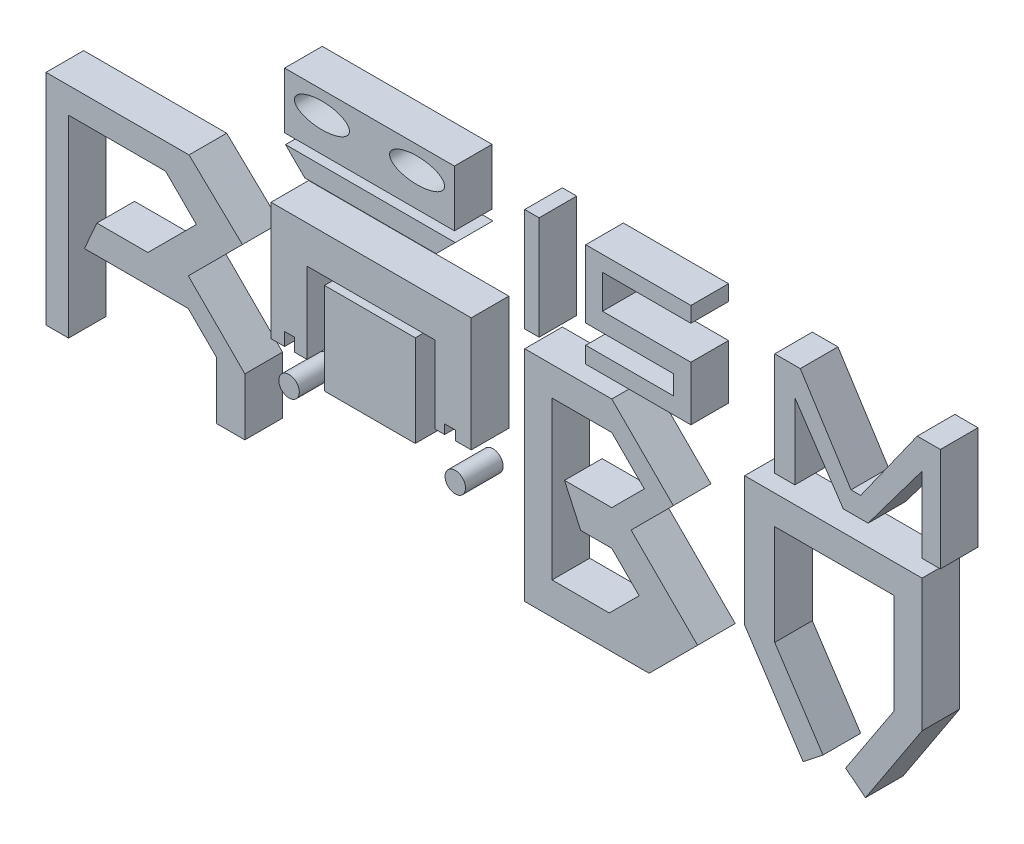
SolidWorks part; units mm, degrees
ref_plane "Front Plane" through (0, 0, 0) normal (0, 0, 1) x (1, 0, 0)
ref_plane "Top Plane" through (0, 0, 0) normal (0, 1, 0) x (1, 0, 0)
ref_plane "Right Plane" through (0, 0, 0) normal (1, 0, 0) x (0, 0, -1)
sketch "Sketch1" plane through (0, 0, 0) normal (0, 0, 1) x (1, 0, 0)
  line L0 (-173.1174, 48.4087) -> (-173.1174, -9.7478)
  line L1 (-173.1174, 48.4087) -> (-135.1174, 48.4087)
  line L2 (-135.1174, 48.4087) -> (-120.9239, 34.8761)
  line L3 (-120.9239, 34.8761) -> (-135.313, 20.487)
  line L4 (-135.313, 20.487) -> (-120.2783, 5.4522)
  line L6 (-120.2783, -9.7478) -> (-127.7957, -9.7478)
  line L7 (-127.7957, -9.7478) -> (-127.7957, 5.4522)
  line L8 (-127.7957, 5.4522) -> (-135.313, 12.9696)
  line L9 (-135.313, 12.9696) -> (-162.9043, 12.9696)
  line L10 (-162.9043, 12.9696) -> (-159.6, 20.487)
  line L11 (-159.6, 20.487) -> (-146.0522, 20.487)
  line L12 (-146.0522, 20.487) -> (-133.1652, 33.3739)
  line L13 (-133.1652, 33.3739) -> (-141.3435, 41.5522)
  line L14 (-141.3435, 41.5522) -> (-167.1174, 41.5522)
  line L15 (-167.1174, 41.5522) -> (-167.1174, -9.7478)
  line L16 (-167.1174, -9.7478) -> (-173.1174, -9.7478)
  line L30 (-113.3391, 48.4087) -> (-113.3391, 17.0174)
  line L35 (-103.7565, 17.0174) -> (-103.7565, 38.4957)
  line L36 (-103.7565, 38.4957) -> (-69.7217, 38.4957)
  line L37 (-69.7217, 38.4957) -> (-69.7217, 18.0087)
  line L38 (-45.9304, 48.4087) -> (-45.9304, -9.7478)
  line L39 (-45.9304, -9.7478) -> (-12.887, -9.7478)
  line L40 (-12.887, -9.7478) -> (0, 3.1391)
  line L41 (0, 3.1391) -> (-17.6783, 20.8174)
  line L42 (-17.6783, 20.8174) -> (-6.4435, 32.0522)
  line L43 (-6.4435, 32.0522) -> (-22.8, 48.4087)
  line L44 (-22.8, 48.4087) -> (-45.9304, 48.4087)
  line L45 (-38.6609, 40.6957) -> (-38.6609, -1.1565)
  line L46 (-38.6609, -1.1565) -> (-23.4609, -1.1565)
  line L47 (-23.4609, -1.1565) -> (-15.5304, 6.7739)
  line L48 (-15.5304, 6.7739) -> (-22.8, 14.0435)
  line L49 (-22.8, 14.0435) -> (-31.0609, 14.0435)
  line L50 (-31.0609, 14.0435) -> (-35.3565, 23.4087)
  line L51 (-35.3565, 23.4087) -> (-22.8, 23.4087)
  line L52 (-22.8, 23.4087) -> (-14.1565, 32.0522)
  line L53 (-14.1565, 32.0522) -> (-22.8, 40.6957)
  line L54 (-22.8, 40.6957) -> (-38.6609, 40.6957)
  line L55 (20.487, 48.4087) -> (22.4696, 48.4087)
  line L56 (59.6304, 48.4087) -> (59.6304, 13.2683)
  line L57 (52.1536, 14.0435) -> (39.3217, -5.4538)
  line L58 (59.6304, 13.2683) -> (44.6087, -9.622)
  line L59 (39.3217, -5.4538) -> (44.6087, -9.622)
  line L60 (52.1536, 14.0435) -> (52.1536, 40.6957)
  line L61 (52.1536, 40.6957) -> (20.487, 40.6957)
  line L62 (33.3188, -5.4538) -> (28.0319, -9.622)
  line L63 (12.5014, 14.0435) -> (28.0319, -9.622)
  line L64 (20.487, 14.0435) -> (33.3188, -5.4538)
  line L65 (20.487, 14.0435) -> (20.487, 40.6957)
  line L66 (12.5014, 48.4087) -> (12.5014, 14.0435)
  line L67 (20.487, 48.4087) -> (22.4696, 48.4087)
  line L69 (12.5014, 48.4087) -> (59.6304, 48.4087)
  line L70 (-60.1391, 18.0087) -> (-60.1391, 48.4087)
  line L71 (-60.1391, 48.4087) -> (-113.3391, 48.4087)
  line L73 (-99.1304, 36.3783) -> (-75.0087, 36.3783)
  line L74 (-99.1304, 36.3783) -> (-99.1304, 12.0609)
  line L76 (-75.0087, 36.3783) -> (-75.0087, 12.0609)
  line L77 (-99.1304, 36.3783) -> (-75.0087, 12.0609) construction
  line L78 (-99.1304, 12.0609) -> (-75.0087, 36.3783) construction
  line L80 (-64.615, 66.1867) -> (-109.7194, 66.1867)
  line L82 (-109.7194, 66.1867) -> (-109.7194, 81.0947)
  line L83 (-109.7194, 81.0947) -> (-64.615, 81.0947)
  line L84 (-64.615, 81.0947) -> (-64.615, 66.1867)
  line L136 (-120.2783, 5.4522) -> (-120.2783, -9.7478)
  line L142 (-99.1304, 12.0609) -> (-75.0087, 12.0609)
  line L148 (-113.3391, 17.0174) -> (-109.7194, 17.0174)
  line L149 (-109.7194, 17.0174) -> (-109.7194, 20.487)
  line L150 (-109.7194, 20.487) -> (-107.1194, 20.487)
  line L151 (-107.1194, 20.487) -> (-107.1194, 17.0174)
  line L152 (-107.1194, 17.0174) -> (-103.7565, 17.0174)
  line L153 (-69.7217, 18.0087) -> (-67.215, 18.0087)
  line L154 (-67.215, 18.0087) -> (-67.215, 20.487)
  line L155 (-67.215, 20.487) -> (-64.3783, 20.487)
  line L156 (-64.3783, 20.487) -> (-64.3783, 18.0087)
  line L157 (-64.3783, 18.0087) -> (-60.1391, 18.0087)
  line L194 (-109.4827, 63.6006) -> (-64.3783, 63.6006)
  line L195 (-64.3783, 63.6006) -> (-69.4851, 58.4939)
  line L196 (-109.4827, 63.6006) -> (-104.3759, 58.4939)
  line L197 (-104.3759, 58.4939) -> (-69.4851, 58.4939)
  line L198 (-45.9304, 80.4444) -> (-45.9304, 52.9589)
  line L199 (-45.9304, 52.9589) -> (-42.1109, 52.9589)
  line L200 (-42.1109, 52.9589) -> (-42.1109, 80.4444)
  line L201 (-42.1109, 80.4444) -> (-45.9304, 80.4444)
  line L214 (-1.7839, 80.4444) -> (-29.7199, 80.4444)
  line L215 (-29.7199, 80.4444) -> (-29.7199, 62.4212)
  line L217 (-1.7839, 80.4444) -> (-1.7839, 76.3303)
  line L218 (-25.2592, 67.37) -> (-1.7839, 67.37)
  line L219 (-1.7839, 67.37) -> (-1.7839, 52.9589)
  line L220 (-1.7839, 52.9589) -> (-29.7199, 52.9589)
  line L221 (-1.7839, 76.3303) -> (-25.2592, 76.3303)
  line L222 (-25.2592, 76.3303) -> (-25.2592, 67.37)
  line L223 (-29.7199, 62.4212) -> (-6.4435, 62.4212)
  line L224 (-6.4435, 62.4212) -> (-6.4435, 57.3144)
  line L225 (-6.4435, 57.3144) -> (-29.7199, 57.3144)
  line L226 (-29.7199, 57.3144) -> (-29.7199, 52.9589)
  line L227 (20.487, 80.4444) -> (20.487, 52.9589)
  line L228 (20.487, 52.9589) -> (25.8368, 52.9589)
  line L231 (38.701, 53.8826) -> (45.3002, 53.8826)
  line L234 (59.6304, 52.9589) -> (64.4967, 52.9589)
  line L235 (64.4967, 52.9589) -> (64.4967, 80.4444)
  line L236 (64.4967, 80.4444) -> (58.3494, 80.4444)
  line L237 (25.8368, 52.9589) -> (25.8368, 73.0259)
  line L238 (25.8368, 73.0259) -> (38.701, 53.8826)
  line L239 (45.3002, 53.8826) -> (59.6304, 73.0259)
  line L240 (59.6304, 73.0259) -> (59.6304, 52.9589)
  line L241 (40.763, 59.2896) -> (43.3277, 59.2896)
  line L242 (43.3277, 59.2896) -> (58.3494, 80.4444)
  line L243 (40.763, 59.2896) -> (27.2781, 80.4444)
  line L244 (27.2781, 80.4444) -> (20.487, 80.4444)
  circle A7 centre (-108.5375, 8.4762) radius 2.719
  circle A8 centre (-108.5375, 8.4762) radius 2.719
  circle A9 centre (-64.3783, 8.4762) radius 2.719
  ellipse E0 centre (-99.8063, 75.1469) end of major axis (-92.4933, 75.1469) minor radius 3.3043
  ellipse E1 centre (-74.528, 75.1469) end of major axis (-81.8411, 75.1469) minor radius 3.3043
  point P19 (-78.9739, 30.0848)
  point P20 (0, 0)
  point P78 (36.3203, 40.6957)
  point P92 (0, 0)
  point P93 (0, 0)
  point P128 (-102.2469, 5.7226)
  dimension "D1" = 38
  dimension "D2" = 6
extrude "Boss-Extrude3" add sketch "Sketch1" along normal mid plane 10 contours L136 L4 L3 L2 L1 L0 L16 L15 L14 L13 L12 L11 L10 L9 L8 L7 L6 | L156 L157 L70 L71 L30 L148 L149 L150 L151 L152 L35 L36 L37 L153 L154 L155 | L74 L142 L76 L73 | L43 L44 L38 L39 L40 L41 L42 L54 L53 L52 L51 L50 L49 L48 L47 L46 L45 | L69 L66 L63 L62 L64 L65 L61 L60 L57 L59 L58 L56 L55 | L243 L244 L227 L228 L237 L238 L231 L239 L240 L234 L235 L236 L242 L241 | L225 L226 L220 L219 L218 L222 L221 L217 L214 L215 L223 L224 | L200 L201 L198 L199 | L84 L83 L82 L80 E0 E1 | A7 | A9 | L194 L195 L197 L196
